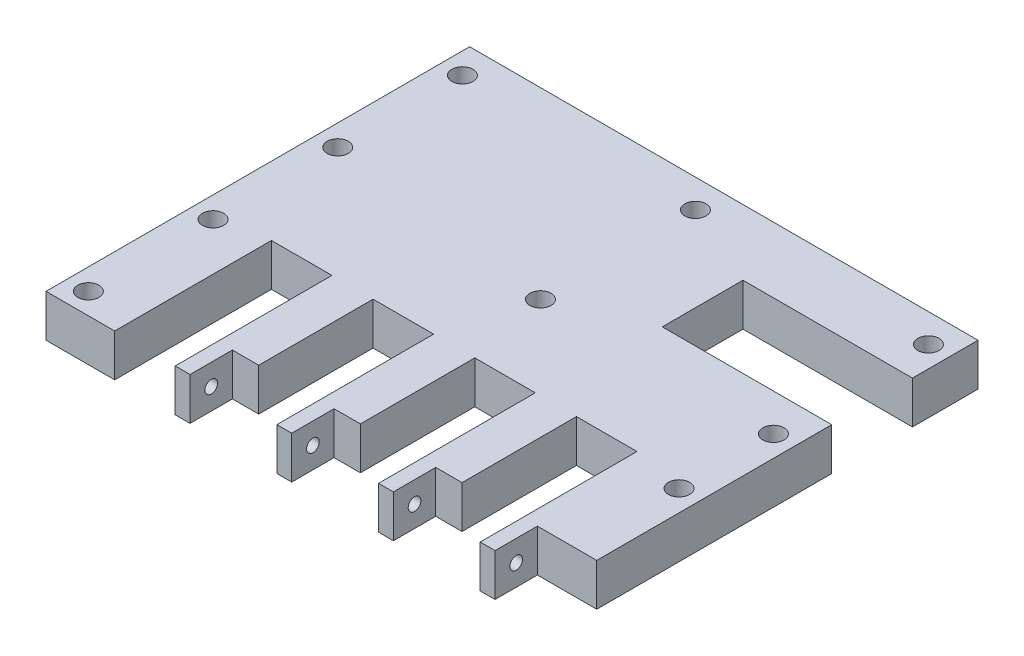
SolidWorks part; units mm, degrees
material "Plain Carbon Steel"
ref_plane "Front Plane" through (0, 0, 0) normal (0, 0, 1) x (1, 0, 0)
ref_plane "Top Plane" through (0, 0, 0) normal (0, 1, 0) x (1, 0, 0)
ref_plane "Right Plane" through (0, 0, 0) normal (1, 0, 0) x (0, 0, -1)
sketch "Sketch1" plane through (0, 0, 0) normal (0, 1, 0) x (1, 0, 0)
  line L1 (60, -50) -> (-60, -50)
  line L2 (60, -50) -> (60, 50)
  line L3 (60, 50) -> (-60, 50)
  line L4 (-60, -50) -> (-60, 50)
  line L5 (60, -50) -> (-60, 50) construction
  line L6 (60, 50) -> (-60, -50) construction
  point P0 (0, 0)
  dimension "D1" = 120
  dimension "D2" = 100
extrude "Boss-Extrude1" add sketch "Sketch1" along normal blind 10
sketch "Sketch2" plane through (0, 0, 50) normal (0, 0, 1) x (1, 0, 0)
  line L0 (-60, 0) -> (60, 0) construction
  line L1 (60, 10) -> (-60, 10) construction
  line L2 (-18.5, 10) -> (-18.5, 0) construction
  line L3 (-42.5, 10) -> (-43.7875, 10)
  line L4 (-29.5, -10) -> (-42.5, -10)
  line L5 (-29.5, -10) -> (-29.5, 10)
  line L6 (-29.5, 10) -> (-42.5, 10)
  line L7 (-42.5, 0) -> (-42.5, 10) construction
  line L8 (-29.5, -10) -> (-42.5, 10) construction
  line L9 (-29.5, 10) -> (-42.5, -10) construction
  line L10 (-5.5, -10) -> (-18.5, -10)
  line L11 (-5.5, -10) -> (-5.5, 10)
  line L12 (-5.5, 10) -> (-18.5, 10)
  line L13 (-18.5, 0) -> (-18.5, 10) construction
  line L14 (-5.5, -10) -> (-18.5, 10) construction
  line L15 (-5.5, 10) -> (-18.5, -10) construction
  line L16 (18.5, -10) -> (5.5, -10)
  line L17 (18.5, -10) -> (18.5, 10)
  line L18 (18.5, 10) -> (5.5, 10)
  line L19 (5.5, 0) -> (5.5, 10) construction
  line L20 (18.5, -10) -> (5.5, 10) construction
  line L21 (18.5, 10) -> (5.5, -10) construction
  line L22 (42.5, -10) -> (29.5, -10)
  line L23 (42.5, -10) -> (42.5, 10)
  line L24 (42.5, 10) -> (29.5, 10)
  line L25 (29.5, 0) -> (29.5, 10) construction
  line L26 (42.5, -10) -> (29.5, 10) construction
  line L27 (42.5, 10) -> (29.5, -10) construction
  line L28 (-42.5, 10) -> (-42.5, 0) construction
  line L29 (60, 0) -> (-60, 0) construction
  line L30 (-42.5, -10) -> (-43.7875, -10)
  line L31 (-43.7875, 10) -> (-43.7875, -10)
  line L32 (-18.5, 10) -> (-19.7875, 10)
  line L33 (-19.7875, 10) -> (-19.7875, -10)
  line L34 (-18.5, -10) -> (-19.7875, -10)
  line L35 (5.5, 10) -> (5.5, 0) construction
  line L36 (5.5, 10) -> (4.2125, 10)
  line L37 (4.2125, 10) -> (4.2125, -10)
  line L38 (5.5, -10) -> (4.2125, -10)
  line L39 (29.5, 10) -> (29.5, 0) construction
  line L40 (29.5, 10) -> (28.2125, 10)
  line L41 (28.2125, 10) -> (28.2125, -10)
  line L42 (29.5, -10) -> (28.2125, -10)
  line L43 (-42.5, -10) -> (-42.5, 0) construction
  line L44 (-42.5, 0) -> (-42.5, -10) construction
  line L45 (-18.5, 0) -> (-18.5, -10) construction
  line L46 (-18.5, -10) -> (-18.5, 0) construction
  line L47 (5.5, -10) -> (5.5, 0) construction
  line L48 (5.5, 0) -> (5.5, -10) construction
  line L49 (29.5, 0) -> (29.5, -10) construction
  line L50 (29.5, -10) -> (29.5, 0) construction
  point P7 (-36, 0)
  point P8 (-12, 0)
  point P9 (12, 0)
  point P10 (36, 0)
  point P11 (-36, 0)
  point P16 (-12, 0)
  point P21 (12, 0)
  point P26 (36, 0)
  point P33 (0, 0)
  dimension "D1" = 120
  dimension "D2" = 14.2875
  dimension "D3" = 13
  dimension "D4" = 4
extrude "Cut-Extrude1" cut sketch "Sketch2" against normal blind 37
sketch "Sketch3" plane through (0, 0, 50) normal (0, 0, 1) x (1, 0, 0)
  line L0 (60, 10) -> (60, 0) construction
  line L1 (-19.7875, 0) -> (-26, 0)
  line L2 (-19.7875, 0) -> (-19.7875, 10)
  line L3 (-19.7875, 10) -> (-26, 10)
  line L4 (-26, 0) -> (-26, 10)
  line L5 (4.2125, 0) -> (-2, 0)
  line L6 (4.2125, 0) -> (4.2125, 10)
  line L7 (4.2125, 10) -> (-2, 10)
  line L8 (-2, 0) -> (-2, 10)
  line L9 (28.2125, 0) -> (22, 0)
  line L10 (28.2125, 0) -> (28.2125, 10)
  line L11 (28.2125, 10) -> (22, 10)
  line L12 (22, 0) -> (22, 10)
  line L13 (46, 0) -> (60, 0)
  line L14 (46, 0) -> (46, 10)
  line L15 (46, 10) -> (60, 10)
  line L16 (60, 0) -> (60, 10)
  line L17 (60, 0) -> (42.5, 0) construction
  line L19 (4.2125, 0) -> (-5.5, 0) construction
  line L21 (-29.5, 0) -> (-29.5, 10) construction
  line L22 (-5.5, 0) -> (-5.5, 10) construction
  line L23 (42.5, 0) -> (42.5, 10) construction
  line L24 (18.5, 0) -> (18.5, 10) construction
  line L25 (-19.7875, 0) -> (-5.5, 0) construction
  line L29 (-19.7875, 10) -> (-29.5, 10) construction
  line L33 (4.2125, 10) -> (-5.5, 10) construction
  line L34 (28.2125, 10) -> (18.5, 10) construction
  line L35 (60, 10) -> (42.5, 10) construction
  dimension "D1" = 3.5
  dimension "D2" = 3.5
  dimension "D3" = 3.5
  dimension "D4" = 3.5
extrude "Cut-Extrude2" cut sketch "Sketch3" against normal blind 10
sketch "Sketch4" plane through (46, 0, 0) normal (1, 0, 0) x (0, 0, -1)
  line L1 (-40, 0) -> (-50, 0) construction
  line L2 (-50, 10) -> (-50, 0) construction
  circle A0 centre (-45, 5) radius 1.5
  dimension "D1" = 3
  dimension "D2" = 5
  dimension "D3" = 5
extrude "Cut-Extrude3" cut sketch "Sketch4" against normal up to surface (75.5 mm away) up to face at (-29.5, 5, 31.5)
sketch "Sketch7" plane through (0, 10, 0) normal (0, 1, 0) x (1, 0, 0)
  line L0 (60, -40) -> (60, 50) construction
  line L1 (60, 34.525) -> (20, 34.525)
  line L2 (60, 34.525) -> (60, 15.475)
  line L3 (60, 15.475) -> (20, 15.475)
  line L4 (20, 34.525) -> (20, 15.475)
  line L5 (60, 50) -> (-60, 50) construction
  line L7 (0, 43.2875) -> (55, 43.2875) construction
  line L8 (0, 43.2875) -> (0, 6.7125) construction
  line L9 (0, 6.7125) -> (55, 6.7125) construction
  line L10 (55, 43.2875) -> (55, 6.7125) construction
  circle A0 centre (55, 6.7125) radius 2.5
  circle A1 centre (55, 43.2875) radius 2.5
  circle A2 centre (0, 43.2875) radius 2.5
  circle A3 centre (0, 6.7125) radius 2.5
  point P6 (60, 25)
  point P17 (20, 25)
  point P18 (0, 25)
  dimension "D5" = 5
  dimension "25" = 25
  dimension "D2" = 19.05
  dimension "D3" = 40
  dimension "D4" = 5
  dimension "D6" = 36.575
extrude "Cut-Extrude4" cut sketch "Sketch7" against normal blind 20
sketch "Sketch10" plane through (0, 10, 0) normal (0, 1, 0) x (1, 0, 0)
  line L0 (-60, -50) -> (-60, 50) construction
  line L5 (-55, 43.2875) -> (55, 43.2875) construction
  line L6 (-55, 43.2875) -> (-55, -45) construction
  line L7 (-55, -45) -> (55, -45) construction
  line L8 (55, 43.2875) -> (55, -45) construction
  line L9 (-43.7875, -50) -> (-60, -50) construction
  line L10 (55, -29.8625) -> (55, 43.2875) construction
  circle A0 centre (55, 43.2875) radius 2.5 construction
  circle A1 centre (-55, 43.2875) radius 2.5
  circle A5 centre (55, 43.2875) radius 2.5
  circle A6 centre (55, 6.7125) radius 2.5
  circle A8 centre (55, 6.7125) radius 2.5 construction
  circle A9 centre (-55, 13.8583) radius 2.5
  circle A10 centre (-55, -15.5708) radius 2.5
  circle A11 centre (-55, -45) radius 2.5
  circle A12 centre (55, -15.5708) radius 2.5
  dimension "D1" = 5
  dimension "D2" = 5
  dimension "D3" = 4
extrude "Cut-Extrude5" cut sketch "Sketch10" against normal up to next (10 mm away)
hole_wizard "Ø5.0mm Dowel Hole1" positions "Sketch11" profile "Sketch12" hole size "Ø5.0" standard "ISO"
sketch "Sketch11" plane through (-676.2935, 10, -1303.2827) normal (0, 1, 0) x (1, 0, 0)
  point P4 (731.2935, -1318.8535)
  point P6 (621.2935, -1318.8535)
  point P9 (621.2935, -1348.2827)
  point P12 (621.2935, -1259.9952)
  point P15 (731.2935, -1259.9952)
  point P18 (731.2935, -1296.5702)
  point P26 (621.2935, -1289.4244)
sketch "Sketch12" plane through (55, 10, 15.5708) normal (1, 0, 0) x (0, 0, 1)
  line L0 (0, 0) -> (0, 26.5022)
  line L1 (0, 26.5022) -> (2.5, 25)
  line L2 (2.5, 25) -> (2.5, 0)
  line L3 (2.5, 0) -> (0, 0)
  line L4 (0, 26.5022) -> (-2.5, 25) construction
  line L5 (0, -6.35) -> (0, 107.95) construction
  dimension "Hole Dia." = 5
  dimension "Hole Depth" = 25
  dimension "Drill Angle" = 118
